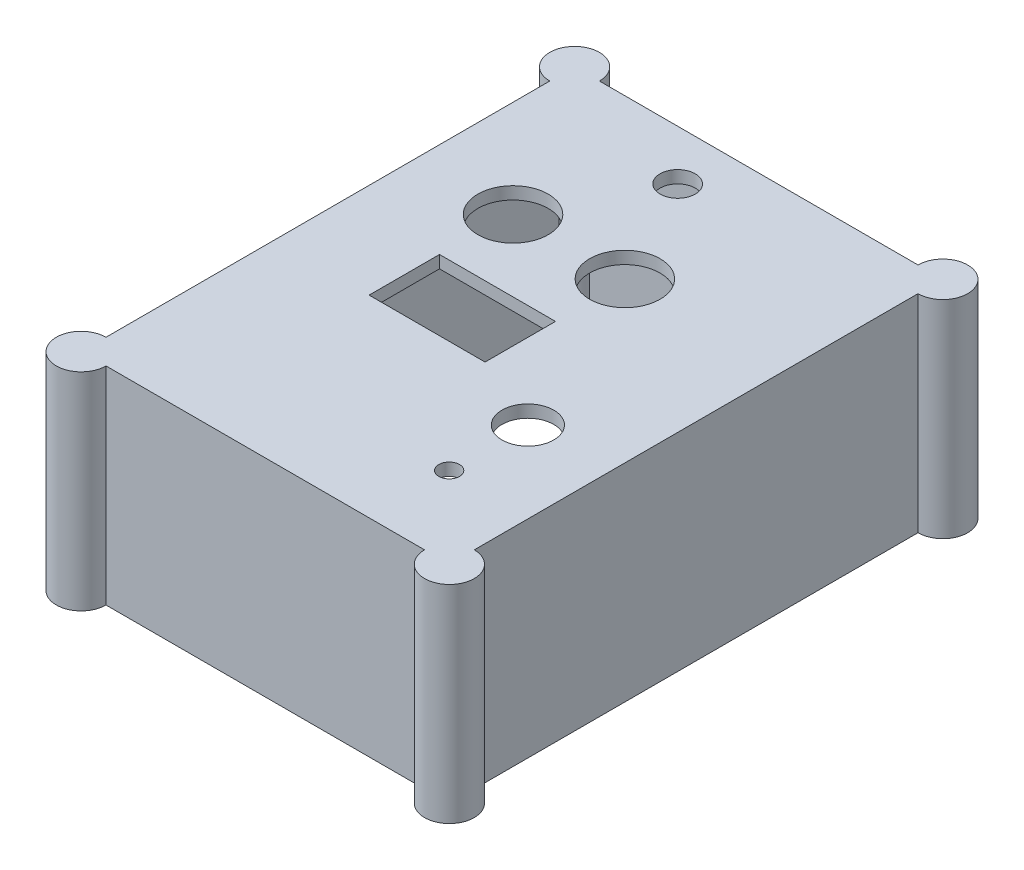
SolidWorks part; units mm, degrees
ref_plane "Front Plane" through (0, 0, 0) normal (0, 0, 1) x (1, 0, 0)
ref_plane "Top Plane" through (0, 0, 0) normal (0, 1, 0) x (1, 0, 0)
ref_plane "Right Plane" through (0, 0, 0) normal (1, 0, 0) x (0, 0, -1)
sketch "Sketch1" plane through (0, 0, 0) normal (0, 1, 0) x (1, 0, 0)
  line L0 (-7.5, 47.5) -> (-7.5, -76.3454) construction
  line L1 (-42.5, -57.5) -> (42.5, -57.5)
  line L2 (-42.5, -57.5) -> (-42.5, 57.5)
  line L3 (-42.5, 57.5) -> (42.5, 57.5)
  line L4 (42.5, -57.5) -> (42.5, 57.5)
  line L5 (-42.5, -57.5) -> (42.5, 57.5) construction
  line L6 (-42.5, 57.5) -> (42.5, -57.5) construction
  line L7 (-28.8128, 31.5) -> (13.8128, 31.5) construction
  line L8 (-31.5875, 11) -> (17.0251, 11) construction
  line L9 (-46.9325, 4) -> (66.3313, 4) construction
  line L10 (-21.5, -13) -> (6.5, -13)
  line L11 (-21.5, -13) -> (-21.5, 4)
  line L12 (-21.5, 4) -> (6.5, 4)
  line L13 (6.5, -13) -> (6.5, 4)
  line L14 (-21.5, -13) -> (6.5, 4) construction
  line L15 (-21.5, 4) -> (6.5, -13) construction
  circle A0 centre (-7.5, 47.5) radius 4.25
  circle A1 centre (-21, 21.25) radius 8.5
  circle A3 centre (6, 21.25) radius 8.5
  circle A4 centre (24.8303, -21) radius 6.25
  circle A6 centre (24.8303, -40) radius 2.5
  point P0 (0, 0)
  point P12 (-7.5, 31.5)
  point P18 (-7.5, -4.5)
  dimension "D3" = 8.5
  dimension "D8" = 17
  dimension "D9" = 27
  dimension "D15" = 19
  dimension "D16" = 5
  dimension "D17" = 12.5
  dimension "D1" = 115
  dimension "D2" = 85
  dimension "D4" = 10
  dimension "D5" = 35
  dimension "D6" = 16
  dimension "D7" = 10.25
  dimension "D10" = 7
  dimension "D11" = 10.25
  dimension "D12" = 17
  dimension "D13" = 28
  dimension "D14" = 20
  dimension "D18" = 25
extrude "Boss-Extrude1" add sketch "Sketch1" along normal blind 3
sketch "Sketch2" plane through (0, 3, 0) normal (0, 1, 0) x (1, 0, 0)
  line L0 (-42.5, 57.5) -> (42.5, 57.5)
  line L1 (42.5, 57.5) -> (42.5, -57.5)
  line L2 (42.5, -57.5) -> (-42.5, -57.5)
  line L3 (-42.5, -57.5) -> (-42.5, 57.5)
  line L5 (-44.4589, -59.571) -> (44.4589, -59.571)
  line L6 (-44.4589, -59.571) -> (-44.4589, 59.571)
  line L7 (-44.4589, 59.571) -> (44.4589, 59.571)
  line L8 (44.4589, -59.571) -> (44.4589, 59.571)
  line L9 (-44.4589, -59.571) -> (44.4589, 59.571) construction
  line L10 (-44.4589, 59.571) -> (44.4589, -59.571) construction
  point P4 (0, 0)
extrude "Boss-Extrude2" add sketch "Sketch2" against normal blind 50
sketch "Sketch3" plane through (0, 3, 0) normal (0, 1, 0) x (1, 0, 0)
  circle A0 centre (44.4589, 59.571) radius 6
  circle A1 centre (-44.4589, 59.571) radius 6
  circle A2 centre (44.4589, -59.571) radius 6
  circle A3 centre (-44.4589, -59.571) radius 6
extrude "Boss-Extrude3" add sketch "Sketch3" against normal blind 50
sketch "Sketch5" plane through (0, -47, 0) normal (0, -1, 0) x (1, 0, 0)
  circle A0 centre (-44.4589, 59.571) radius 1.6
  circle A1 centre (44.4589, 59.571) radius 1.6
  circle A2 centre (44.4589, -59.571) radius 1.6
  circle A3 centre (-44.4589, -59.571) radius 1.6
  dimension "D1" = 3.2
extrude "Cut-Extrude1" cut sketch "Sketch5" against normal blind 30
